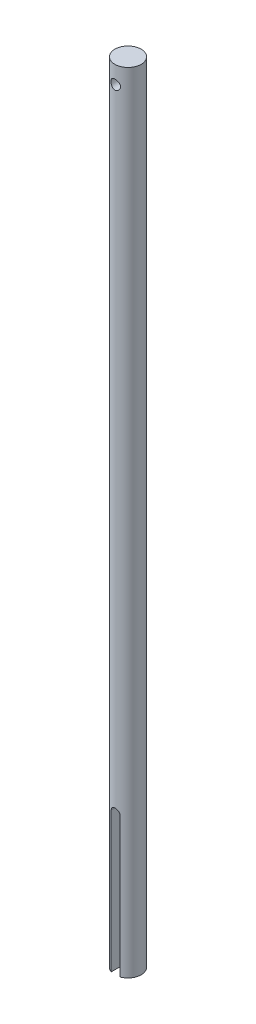
SolidWorks part; units mm, degrees
ref_plane "Front" through (0, 0, 0) normal (0, 0, 1) x (1, 0, 0)
ref_plane "Top" through (0, 0, 0) normal (0, 1, 0) x (1, 0, 0)
ref_plane "Right" through (0, 0, 0) normal (1, 0, 0) x (0, 0, -1)
sketch "Sketch1" plane through (0, 0, 0) normal (0, 1, 0) x (1, 0, 0)
  circle A0 centre (0, 0) radius 4.7625
  dimension "D1" = 9.525
extrude "Boss-Extrude1" add sketch "Sketch1" along normal blind 285.75
sketch "Sketch2" plane through (0, 0, 0) normal (0, 0, 1) x (1, 0, 0)
  line L0 (0, -50.8) -> (0, 50.8) construction
  line L1 (-1.5875, -50.8) -> (-1.5875, 50.8)
  line L2 (1.5875, -50.8) -> (1.5875, 50.8)
  line L3 (-4.7625, 0) -> (4.7625, 0) construction
  arc A0 (-1.5875, -50.8) -> (1.5875, -50.8) centre (0, -50.8) ccw
  arc A1 (1.5875, 50.8) -> (-1.5875, 50.8) centre (0, 50.8) ccw
  point P2 (0, 0)
  point P10 (0, 52.3875)
  dimension "D1" = 52.3875
  dimension "D2" = 3.175
extrude "Cut-Extrude1" cut sketch "Sketch2" against normal through all both and the other way through all
ref_plane "Plane1" through (0, 0, -4.7625) normal (0, 0, -1) x (-1, 0, 0)
hole_wizard "#8-32 Tapped Hole1" positions "Sketch5" profile "Sketch7" tap size "#8-32" standard "ANSI Inch" end condition through all
sketch "Sketch5" plane through (0, 0, -4.7625) normal (0, 0, -1) x (-1, 0, 0)
  line L1 (4.7625, 285.75) -> (-4.7625, 285.75) construction
  point P7 (0, 279.4)
  dimension "D2" = 6.35
sketch "Sketch7" plane through (0, 279.4, -4.7625) normal (1, 0, 0) x (0, 1, 0)
  line L0 (0, 0) -> (0, 9.525)
  line L1 (0, 9.525) -> (1.7272, 9.525)
  line L2 (1.7272, 9.525) -> (1.7272, 0)
  line L5 (1.7272, 0) -> (0, 0)
  line L11 (0, -6.35) -> (0, 107.95) construction
  dimension "Thru Tap Drill Dia." = 3.4544
  dimension "Thru Tap Drill Depth" = 9.525
cosmetic thread "Hole Thread1" parameters "D2"=4.1656
